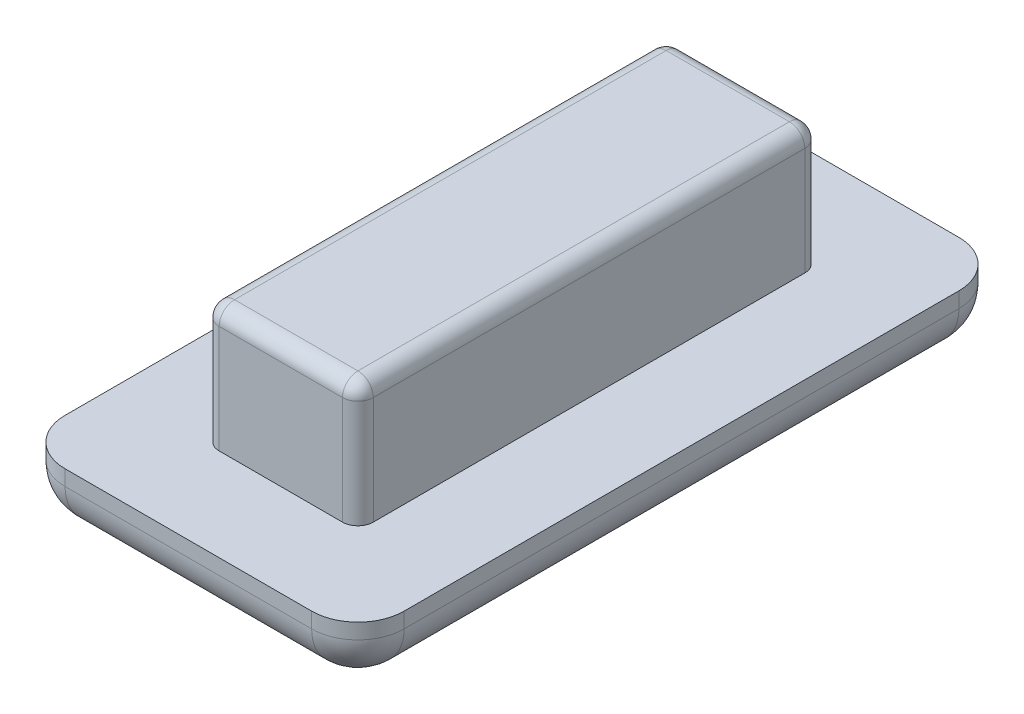
SolidWorks part; units mm, degrees
ref_plane "Front Plane" through (0, 0, 0) normal (0, 0, 1) x (1, 0, 0)
ref_plane "Top Plane" through (0, 0, 0) normal (0, 1, 0) x (1, 0, 0)
ref_plane "Right Plane" through (0, 0, 0) normal (1, 0, 0) x (0, 0, -1)
sketch "Sketch1" plane through (0, 0, 0) normal (0, 1, 0) x (1, 0, 0)
  line L0 (6, 0) -> (0, 0) construction
  line L1 (6, 16) -> (6, 0) construction
  line L2 (0, 0) -> (0, 16) construction
  line L3 (0, 16) -> (6, 16) construction
  line L4 (6, 0) -> (0, 0) construction
  line L5 (6, 16) -> (6, 0) construction
  line L6 (0, 0) -> (0, 16) construction
  line L7 (0, 16) -> (6, 16) construction
  line L8 (6, 16) -> (0, 0) construction
  line L10 (5.5, 0.5) -> (0.5, 0.5)
  line L11 (5.5, 0.5) -> (5.5, 15.5)
  line L12 (5.5, 15.5) -> (0.5, 15.5)
  line L13 (0.5, 0.5) -> (0.5, 15.5)
  line L14 (5.5, 0.5) -> (0.5, 15.5) construction
  line L15 (5.5, 15.5) -> (0.5, 0.5) construction
  point P3 (3, 8)
  dimension "D1" = 0.5
  dimension "D2" = 0.5
extrude "Boss-Extrude1" add sketch "Sketch1" along normal blind 4
sketch "Sketch2" plane through (0, 0, 0) normal (0, -1, 0) x (1, 0, 0)
  line L0 (5.5, -0.5) -> (0.5, -15.5) construction
  line L1 (5.5, -0.5) -> (5.5, -15.5) construction
  line L2 (-2.5, 2.5) -> (8.5, 2.5)
  line L3 (-2.5, 2.5) -> (-2.5, -18.5)
  line L4 (-2.5, -18.5) -> (8.5, -18.5)
  line L5 (8.5, 2.5) -> (8.5, -18.5)
  line L6 (-2.5, 2.5) -> (8.5, -18.5) construction
  line L7 (-2.5, -18.5) -> (8.5, 2.5) construction
  line L8 (0.5, -0.5) -> (5.5, -0.5) construction
  point P4 (3, -8)
  dimension "D1" = 3
  dimension "D2" = 3
extrude "Boss-Extrude2" add sketch "Sketch2" along normal blind 2
fillet "Fillet1" radius 0.5 8 edges at (3, 4, -15.5) (5.5, 4, -8) (3, 4, -0.5) (0.5, 4, -8) (0.5, 2, -15.5) (5.5, 2, -15.5) (0.5, 2, -0.5) (5.5, 2, -0.5)
fillet "Fillet2" radius 1.5 8 edges at (3, -2, -18.5) (-2.5, -2, -8) (3, -2, 2.5) (8.5, -2, -8) (-2.5, -1, 2.5) (-2.5, -1, -18.5) (8.5, -1, -18.5) (8.5, -1, 2.5)
